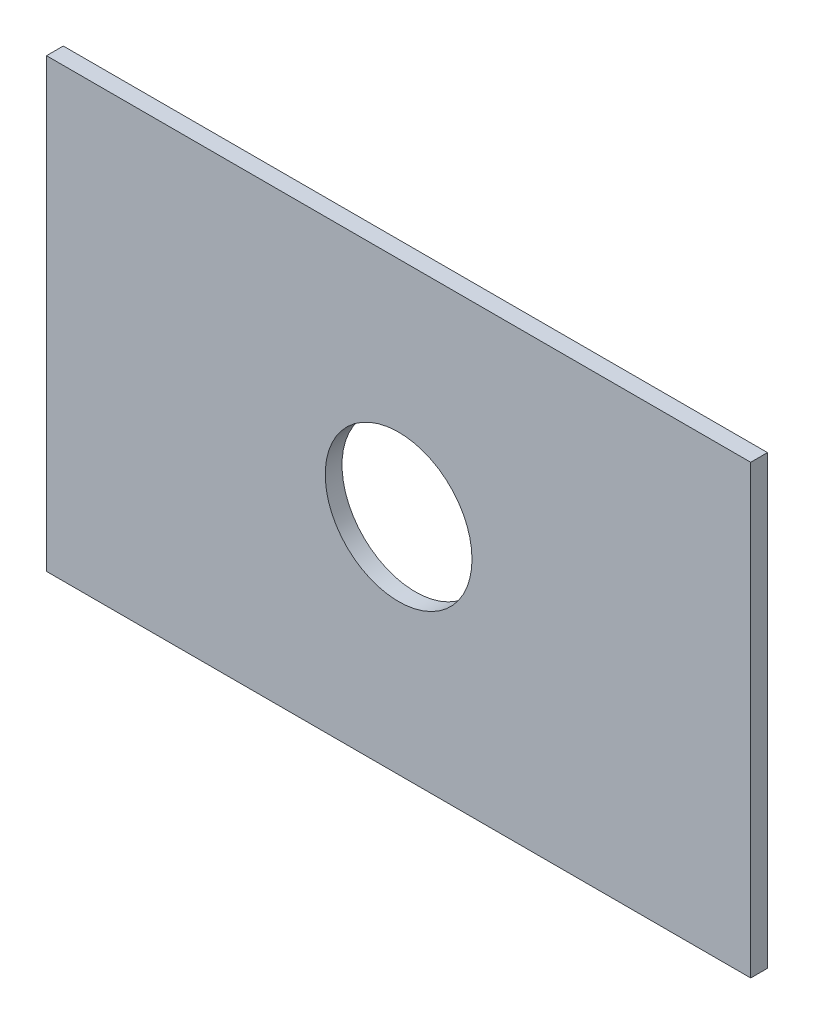
SolidWorks part; units mm, degrees
ref_plane "Front Plane" through (0, 0, 0) normal (0, 0, 1) x (1, 0, 0)
ref_plane "Top Plane" through (0, 0, 0) normal (0, 1, 0) x (1, 0, 0)
ref_plane "Right Plane" through (0, 0, 0) normal (1, 0, 0) x (0, 0, -1)
sketch "Sketch1" plane through (0, 0, 0) normal (0, 0, 1) x (1, 0, 0)
  line L1 (-53.3136, -33.8131) -> (53.3136, -33.8131)
  line L2 (-53.3136, -33.8131) -> (-53.3136, 33.8131)
  line L3 (-53.3136, 33.8131) -> (53.3136, 33.8131)
  line L4 (53.3136, -33.8131) -> (53.3136, 33.8131)
  line L5 (-53.3136, -33.8131) -> (53.3136, 33.8131) construction
  line L6 (-53.3136, 33.8131) -> (53.3136, -33.8131) construction
  circle A0 centre (0, 0) radius 11.1125
  point P0 (0, 0)
  dimension "D1" = 22.225
extrude "Boss-Extrude1" add sketch "Sketch1" along normal blind 2.54
